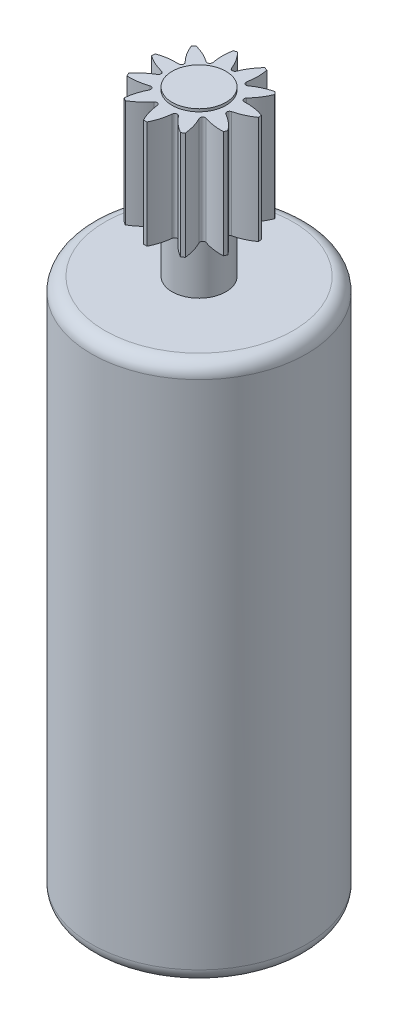
SolidWorks part; units mm, degrees
ref_plane "Front Plane" through (0, 0, 0) normal (0, 0, 1) x (1, 0, 0)
ref_plane "Top Plane" through (0, 0, 0) normal (0, 1, 0) x (1, 0, 0)
ref_plane "Right Plane" through (0, 0, 0) normal (1, 0, 0) x (0, 0, -1)
sketch "Sketch1" plane through (0, 0, 0) normal (0, 0, 1) x (1, 0, 0)
  line L0 (0, 0) -> (0, 26.1)
  line L1 (0, 0) -> (4, 0)
  line L2 (4, 0) -> (4, 20)
  line L3 (4, 20) -> (1, 20)
  line L4 (1, 20) -> (1, 22)
  line L5 (1, 22) -> (2, 22)
  line L6 (2, 22) -> (2, 26)
  line L7 (2, 26) -> (1, 26)
  line L8 (1, 26) -> (1, 26.1)
  line L9 (1, 26.1) -> (0, 26.1)
  dimension "D1" = 26.1
  dimension "D2" = 4
  dimension "D3" = 20
  dimension "D4" = 3
  dimension "D5" = 2
  dimension "D6" = 1
  dimension "D7" = 4
revolve "Revolve1" add sketch "Sketch1" angle 360 about L0
fillet "Fillet1" radius 0.5 2 edges at (0, 20, -4) (0, 0, -4)
sketch "Sketch2" plane through (0, 26, 0) normal (0, 1, 0) x (1, 0, 0)
  line L0 (0, 0) -> (0, 2.9979) construction
  circle A0 centre (0, 0) radius 2 construction
  arc A1 (0.5, 1.9365) -> (-0.5, 1.9365) centre (0, 0) ccw
  arc A2 (-0.5, 1.9365) -> (-0.0929, 1.2999) centre (-1.951, 0.5601) cw
  circle A3 centre (0, 0) radius 1 construction
  arc A4 (0.5, 1.9365) -> (0.0929, 1.2999) centre (1.951, 0.5601) ccw
  arc A5 (-0.0929, 1.2999) -> (0.0929, 1.2999) centre (0, 1.3369) ccw
  point P15 (0, 1)
  dimension "D2" = 2
  dimension "D3" = 2
  dimension "D4" = 0.1
  dimension "D1" = 1
extrude "Cut-Extrude1" cut sketch "Sketch2" against normal up to next (4 mm away)
pattern_circular "CirPattern1" count 11 over 360 about axis through (0, 0, 0) along (0, 1, 0) of "Cut-Extrude1"
